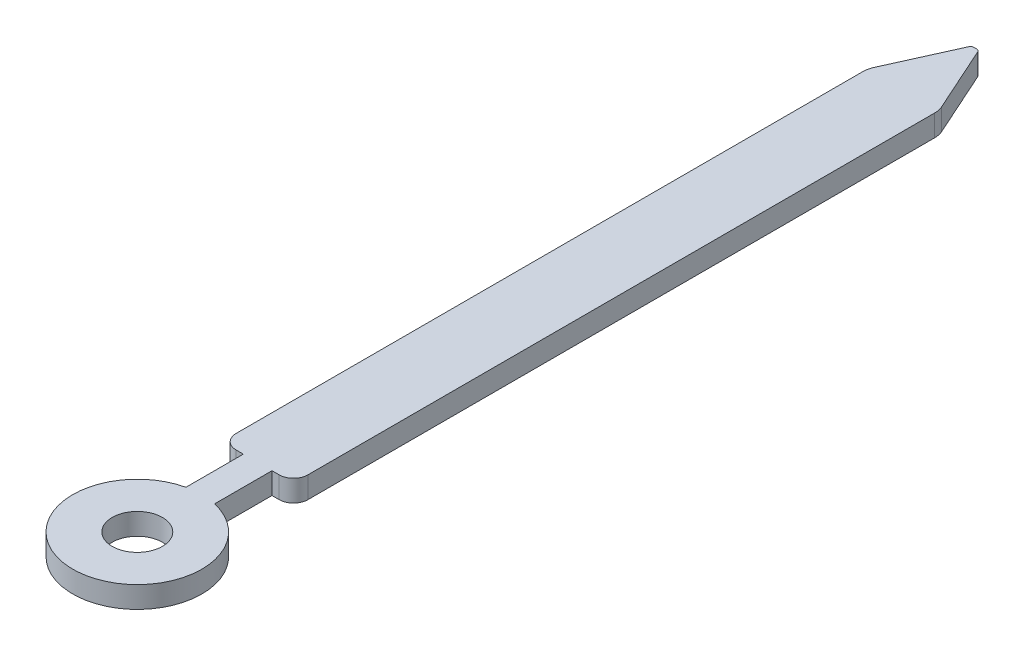
SolidWorks part; units mm, degrees
ref_plane "Front Plane" through (0, 0, 0) normal (0, 0, 1) x (1, 0, 0)
ref_plane "Top Plane" through (0, 0, 0) normal (0, 1, 0) x (1, 0, 0)
ref_plane "Right Plane" through (0, 0, 0) normal (1, 0, 0) x (0, 0, -1)
sketch "Sketch1" plane through (0, 0, 0) normal (0, 1, 0) x (1, 0, 0)
  line L0 (0.063, 9.9711) -> (0.4736, 9.0587)
  line L1 (-0.3, 0) -> (-0.2, 0)
  line L2 (-0.5, 0.2) -> (-0.5, 8.9356)
  line L3 (-0.0183, 10) -> (0.0183, 10)
  line L4 (0.5, 0.2) -> (0.5, 8.9356)
  line L5 (-0.063, 9.9711) -> (-0.4736, 9.0587)
  line L6 (0.2, 0) -> (0.2, -0.8)
  line L7 (-0.2, 0) -> (-0.2, -0.8)
  line L8 (0.2, 0) -> (0.3, 0)
  arc A0 (-0.063, 9.9711) -> (-0.0183, 10) centre (-0.0183, 9.951) cw
  arc A1 (0.063, 9.9711) -> (0.0183, 10) centre (0.0183, 9.951) ccw
  arc A2 (-0.4736, 9.0587) -> (-0.5, 8.9356) centre (-0.2, 8.9356) ccw
  arc A3 (0.4736, 9.0587) -> (0.5, 8.9356) centre (0.2, 8.9356) cw
  arc A4 (-0.2, -0.8) -> (0.2, -0.8) centre (0, -1.6775) ccw
  arc A5 (-0.3, 0) -> (-0.5, 0.2) centre (-0.3, 0.2) cw
  arc A6 (0.3, 0) -> (0.5, 0.2) centre (0.3, 0.2) ccw
  circle A7 centre (0, -1.6775) radius 0.35
  point P9 (-0.05, 10)
  point P12 (0.05, 10)
  point P15 (-0.5, 9)
  point P18 (0.5, 9)
  point P26 (-0.5, 0)
  point P29 (0.5, 0)
  dimension "D3" = 0.049
  dimension "D6" = 0.3
  dimension "D9" = 0.2
  dimension "D1" = 0.5
  dimension "D2" = 1
  dimension "D4" = 1
  dimension "D5" = 1
  dimension "D7" = 0.8
  dimension "D8" = 0.8
extrude "Boss-Extrude1" add sketch "Sketch1" along normal blind 0.3
